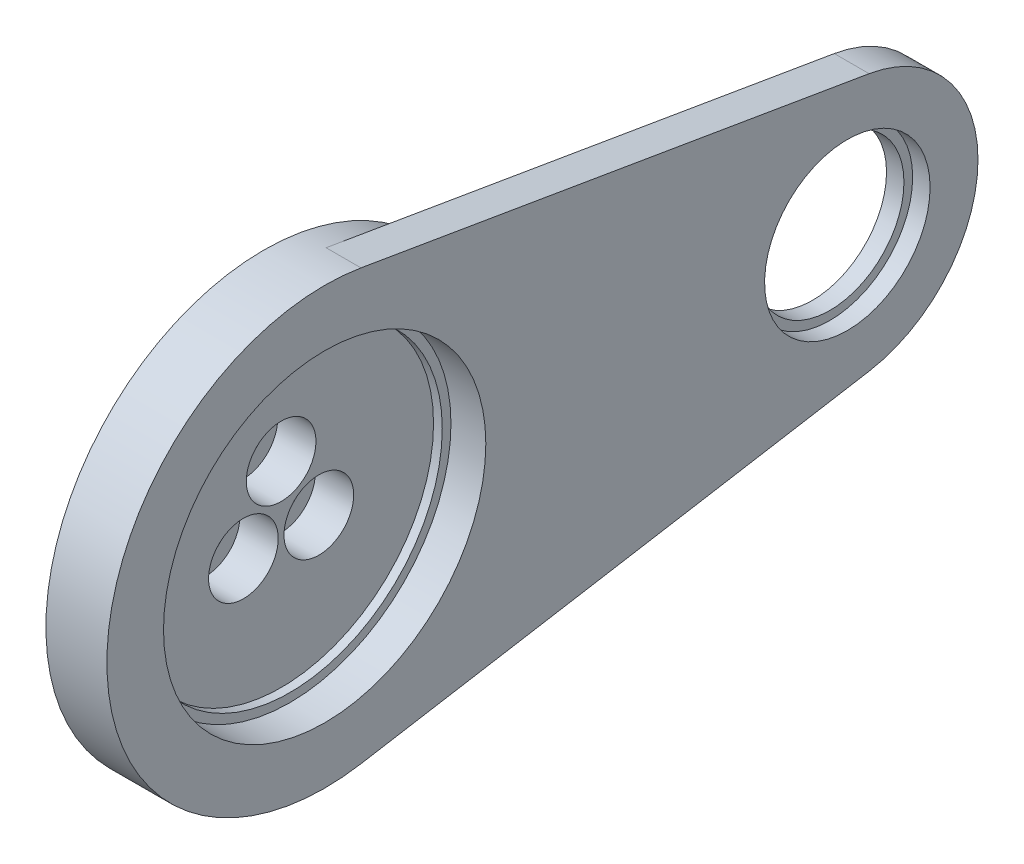
SolidWorks part; units mm, degrees
ref_plane "정면" through (0, 0, 0) normal (0, 0, 1) x (1, 0, 0)
ref_plane "윗면" through (0, 0, 0) normal (0, 1, 0) x (1, 0, 0)
ref_plane "우측면" through (0, 0, 0) normal (1, 0, 0) x (0, 0, -1)
sketch "스케치3" plane through (0, 0, 0) normal (1, 0, 0) x (0, 0, -1)
  circle A0 centre (0, 0) radius 25
  dimension "D1" = 50
extrude "보스-돌출1" add sketch "스케치3" along normal blind 2
sketch "스케치4" plane through (2, 0, 0) normal (1, 0, 0) x (0, 0, -1)
  circle A0 centre (0, 0) radius 17.5
  circle A1 centre (0, 0) radius 25
  circle A2 centre (0, 0) radius 25 construction
  dimension "D1" = 35
extrude "보스-돌출2" add sketch "스케치4" along normal blind 1
sketch "스케치5" plane through (3, 0, 0) normal (1, 0, 0) x (0, 0, -1)
  circle A0 centre (0, 0) radius 18.5
  circle A1 centre (0, 0) radius 25
  circle A2 centre (0, 0) radius 25 construction
  dimension "D1" = 37
extrude "보스-돌출3" add sketch "스케치5" along normal blind 7
sketch "스케치6" plane through (10, 0, 0) normal (1, 0, 0) x (0, 0, -1)
  circle A0 centre (0, 0) radius 25
  circle A1 centre (0, 0) radius 17.5
  dimension "D1" = 35
  dimension "D2" = 50
extrude "보스-돌출4" add sketch "스케치6" along normal blind 2
sketch "스케치10" plane through (12, 0, 0) normal (1, 0, 0) x (0, 0, -1)
  line L0 (0, 0) -> (60, 0) construction
  line L1 (4.1667, 24.6503) -> (62.5, 14.7902)
  line L2 (4.1667, -24.6503) -> (62.5, -14.7902)
  arc A0 (62.5, -14.7902) -> (62.5, 14.7902) centre (60, 0) ccw
  arc A1 (4.1667, -24.6503) -> (4.1667, 24.6503) centre (0, 0) ccw
  circle A2 centre (0, 0) radius 25 construction
  dimension "D1" = 30
  dimension "D2" = 60
extrude "보스-돌출5" add sketch "스케치10" against normal blind 9
ref_plane "평면2" through (7.5, 0, 0) normal (1, 0, 0) x (0, 0, -1)
sketch "스케치11" plane through (7.5, 0, 0) normal (1, 0, 0) x (0, 0, -1)
  circle A0 centre (60, 0) radius 8.5
  arc A1 (62.5, -14.7902) -> (62.5, 14.7902) centre (60, 0) ccw construction
  dimension "D1" = 17
extrude "컷-돌출3" cut sketch "스케치11" against normal mid plane 222
sketch "스케치12" plane through (7.5, 0, 0) normal (1, 0, 0) x (0, 0, -1)
  circle A0 centre (60, 0) radius 9.5
  circle A1 centre (60, 0) radius 8.5 construction
  dimension "D1" = 19
extrude "컷-돌출4" cut sketch "스케치12" against normal mid plane 5
sketch "스케치13" plane through (0, 0, 0) normal (-1, 0, 0) x (0, 0, 1)
  circle A0 centre (0, 0) radius 9.5
  circle A1 centre (0, 0) radius 25 construction
  dimension "D1" = 19
extrude "보스-돌출6" add sketch "스케치13" along normal blind 5
sketch "스케치14" plane through (2, 0, 0) normal (1, 0, 0) x (0, 0, -1)
  circle A0 centre (0, 0) radius 5 construction
  dimension "D1" = 10
hole_wizard "M4 육각 소켓 머리 캡 나사용 카운터보어1" positions "스케치15" profile "스케치16" counterbore size "M4" standard "ISO" end condition through all
sketch "스케치15" plane through (2, 0, 0) normal (1, 0, 0) x (0, 0, -1)
  circle A0 centre (0, 0) radius 5 construction
  point P0 (0, 5)
sketch "스케치16" plane through (2, 5, 0) normal (0, 1, 0) x (0, 0, -1)
  line L0 (0, 0) -> (0, 7)
  line L1 (0, 7) -> (2.25, 7)
  line L3 (2.25, 7) -> (2.25, 4.4)
  line L4 (2.25, 4.4) -> (4, 4.4)
  line L5 (4, 4.4) -> (4, 0)
  line L7 (4, 0) -> (0, 0)
  line L11 (0, -6.35) -> (0, 107.95) construction
  dimension "관통 구멍 지름" = 4.5
  dimension "관통 구멍 깊이" = 7
  dimension "카운터보어 지름" = 8
  dimension "카운터보어 깊이" = 4.4
pattern_circular "원형 패턴1" count 3 over 360 about axis through (0, 0, 0) along (1, 0, 0) of "M4 육각 소켓 머리 캡 나사용 카운터보어1"
sketch "스케치17" plane through (0, 0, 0) normal (0, 0, 1) x (1, 0, 0)
  line L0 (12, -25) -> (12, 25) construction
  line L1 (7, 30.4497) -> (24.7141, 30.4497)
  line L2 (7, 30.4497) -> (7, -34.1546)
  line L3 (7, -34.1546) -> (24.7141, -34.1546)
  line L4 (24.7141, 30.4497) -> (24.7141, -34.1546)
  dimension "D1" = 5
extrude "컷-돌출5" cut sketch "스케치17" against normal mid plane 2222
